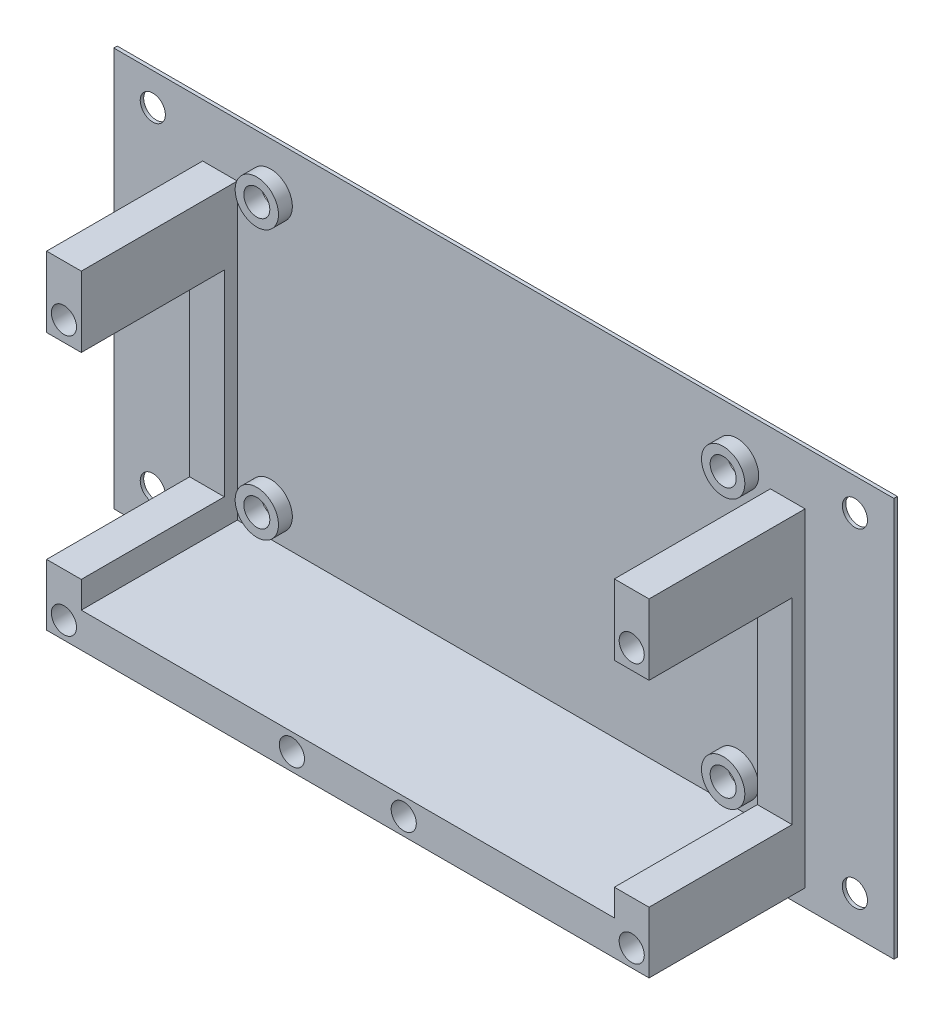
SolidWorks part; units mm, degrees
ref_plane "Ebene vorne" through (0, 0, 0) normal (0, 0, 1) x (1, 0, 0)
ref_plane "Ebene oben" through (0, 0, 0) normal (0, 1, 0) x (1, 0, 0)
ref_plane "Ebene rechts" through (0, 0, 0) normal (1, 0, 0) x (0, 0, -1)
sketch "Skizze1" plane through (0, 0, 0) normal (0, 0, 1) x (1, 0, 0)
  line L1 (-45, -25) -> (45, -25)
  line L2 (-45, -25) -> (-45, 25)
  line L3 (-45, 25) -> (45, 25)
  line L4 (45, -25) -> (45, 25)
  line L5 (-45, -25) -> (45, 25) construction
  line L6 (-45, 25) -> (45, -25) construction
  point P0 (0, 0)
  dimension "D1" = 90
  dimension "D2" = 50
extrude "Aufsatz-Linear austragen1" add sketch "Skizze1" along normal blind 0.4
sketch "Skizze3" plane through (0, 0, 0.4) normal (0, 0, 1) x (1, 0, 0)
  line L1 (-26.9, -11.5381) -> (26.9, -11.5381) construction
  line L2 (-26.9, -11.5381) -> (-26.9, 19.4619) construction
  line L3 (-26.9, 19.4619) -> (26.9, 19.4619) construction
  line L4 (26.9, -11.5381) -> (26.9, 19.4619) construction
  line L5 (-26.9, -11.5381) -> (26.9, 19.4619) construction
  line L6 (-26.9, 19.4619) -> (26.9, -11.5381) construction
  circle A0 centre (-26.9, 19.4619) radius 1.5
  circle A1 centre (26.9, 19.4619) radius 1.5
  circle A2 centre (26.9, -11.5381) radius 1.5
  circle A3 centre (-26.9, -11.5381) radius 1.5
  point P0 (0, 3.9619)
  dimension "D3" = 3
  dimension "D1" = 53.8
  dimension "D2" = 31
extrude "Schnitt-Linear austragen1" cut sketch "Skizze3" against normal through all
sketch "Skizze18" plane through (0, 0, 0.4) normal (0, 0, 1) x (1, 0, 0)
  line L0 (0, 0) -> (0, 9.3339) construction
  line L1 (0, 0) -> (-5.4377, 0) construction
  line L2 (-26.9, 19.4619) -> (-26.9, -11.5381) construction
  line L3 (-26.9, 3.9619) -> (-18.5006, 3.9619) construction
  circle A0 centre (-26.9, 19.4619) radius 2.5
  circle A1 centre (-26.9, 19.4619) radius 1.5
  circle A4 centre (-26.9, 19.4619) radius 1.5 construction
  circle A5 centre (26.9, 19.4619) radius 1.5
  circle A6 centre (26.9, 19.4619) radius 2.5
  circle A7 centre (26.9, -11.5381) radius 2.5
  circle A8 centre (26.9, -11.5381) radius 1.5
  circle A9 centre (-26.9, -11.5381) radius 1.5
  circle A10 centre (-26.9, -11.5381) radius 2.5
  dimension "D1" = 1
extrude "Aufsatz-Linear austragen5" add sketch "Skizze18" along normal blind 1.6
sketch "Skizze4" plane through (0, 0, 0.4) normal (0, 0, 1) x (1, 0, 0)
  line L0 (-26.9, 19.4619) -> (26.9, -11.5381) construction
  line L2 (-30.25, -14.5381) -> (30.25, -14.5381)
  line L3 (-30.25, -14.5381) -> (-30.25, 22.4619)
  line L4 (-30.25, 22.4619) -> (30.25, 22.4619)
  line L5 (30.25, -14.5381) -> (30.25, 22.4619)
  line L6 (-30.25, -14.5381) -> (30.25, 22.4619) construction
  line L7 (-30.25, 22.4619) -> (30.25, -14.5381) construction
  point P4 (0, 3.9619)
  dimension "D1" = 60.5
  dimension "D2" = 37
sketch "Skizze22" plane through (0, 0, 0.4) normal (0, 0, 1) x (1, 0, 0)
  line L0 (30.75, -15.0381) -> (0, -15.0381)
  line L1 (30.75, -15.0381) -> (30.75, -11.9652)
  line L2 (-30.25, -14.5381) -> (30.25, -14.5381) construction
  line L3 (30.25, -14.5381) -> (30.25, 22.4619) construction
  line L5 (0, -19.0381) -> (34.75, -19.0381)
  line L6 (34.75, -19.0381) -> (34.75, -11.9652)
  line L7 (34.75, -11.9652) -> (30.75, -11.9652)
  line L8 (34.75, -19.0381) -> (30.75, -15.0381) construction
  line L9 (32.75, -17.0381) -> (-7.0815, -17.0381) construction
  line L10 (32.75, -17.0381) -> (32.75, 17.6557) construction
  line L11 (34.75, 15.2237) -> (34.75, 18.8333)
  line L13 (34.75, 15.2237) -> (34.75, 10.7001)
  line L14 (34.75, 10.7001) -> (30.75, 10.7001)
  line L15 (30.75, 15.2237) -> (30.75, 10.7001)
  line L16 (34.75, 15.2237) -> (30.75, 10.7001) construction
  line L17 (34.75, 10.7001) -> (30.75, 15.2237) construction
  line L18 (34.75, 18.8333) -> (30.75, 18.8333)
  line L19 (30.75, 18.8333) -> (30.75, 15.2237)
  line L20 (0, 0) -> (0, -7.7771) construction
  line L21 (-34.75, 10.7001) -> (-30.75, 15.2237) construction
  line L22 (-34.75, 15.2237) -> (-30.75, 10.7001) construction
  line L23 (-32.75, -17.0381) -> (-32.75, 17.6557) construction
  line L24 (-34.75, -19.0381) -> (-30.75, -15.0381) construction
  line L25 (-30.75, 18.8333) -> (-30.75, 15.2237)
  line L26 (-34.75, 18.8333) -> (-30.75, 18.8333)
  line L27 (-30.75, 15.2237) -> (-30.75, 10.7001)
  line L28 (-34.75, 10.7001) -> (-30.75, 10.7001)
  line L29 (-34.75, 15.2237) -> (-34.75, 10.7001)
  line L30 (-34.75, 15.2237) -> (-34.75, 18.8333)
  line L31 (-34.75, -11.9652) -> (-30.75, -11.9652)
  line L32 (-34.75, -19.0381) -> (-34.75, -11.9652)
  line L33 (0, -19.0381) -> (-34.75, -19.0381)
  line L35 (-30.75, -15.0381) -> (-30.75, -11.9652)
  line L36 (-30.75, -15.0381) -> (0, -15.0381)
  circle A0 centre (32.75, -17.0381) radius 1.45
  circle A1 centre (6.45, -17.0381) radius 1.45
  circle A2 centre (32.75, 12.9619) radius 1.45
  circle A3 centre (-32.75, 12.9619) radius 1.45
  circle A4 centre (-6.45, -17.0381) radius 1.45
  circle A5 centre (-32.75, -17.0381) radius 1.45
  dimension "D5" = 2.9
  dimension "D1" = 0.5
  dimension "D2" = 0.5
  dimension "D3" = 4
  dimension "D4" = 4
  dimension "D6" = 26.3
  dimension "D7" = 30
extrude "Aufsatz-Linear austragen7" add sketch "Skizze22" along normal blind 18
sketch "Skizze24" plane through (0, 0, 0.4) normal (0, 0, 1) x (1, 0, 0)
  line L0 (-34.75, 10.7001) -> (-34.75, -11.9652)
  line L1 (-34.75, -11.9652) -> (-30.75, -11.9652)
  line L2 (-30.75, -11.9652) -> (-30.75, 10.7001)
  line L3 (-30.75, 10.7001) -> (-34.75, 10.7001)
  line L4 (0, 0) -> (0, 11.0692) construction
  line L5 (30.75, 10.7001) -> (34.75, 10.7001)
  line L6 (30.75, -11.9652) -> (30.75, 10.7001)
  line L7 (34.75, -11.9652) -> (30.75, -11.9652)
  line L8 (34.75, 10.7001) -> (34.75, -11.9652)
extrude "Aufsatz-Linear austragen8" add sketch "Skizze24" along normal blind 1.5
sketch "Skizze23" plane through (0, 0, 0.4) normal (0, 0, 1) x (1, 0, 0)
  line L0 (-43, 23.8) -> (-43, -19.0381)
  line L1 (-43, -19.0381) -> (43, -19.0381)
  line L2 (43, -19.0381) -> (43, 23.8)
  line L3 (43, 23.8) -> (-43, 23.8)
  line L4 (45, 25) -> (-45, 25) construction
  line L5 (-45, 25) -> (-45, -25) construction
  line L7 (45, -25) -> (45, 25) construction
  line L8 (-45, 25) -> (-45, -21.0381)
  line L10 (45, -21.0381) -> (45, 25)
  line L11 (45, 25) -> (-45, 25)
  line L12 (-34.75, -19.0381) -> (34.75, -19.0381) construction
  line L13 (-45, -21.0381) -> (45, -21.0381)
  dimension "D1" = 1.2
  dimension "D2" = 2
  dimension "D3" = 2
  dimension "D4" = 2
extrude "Aufsatz-Linear austragen9" [suppressed] add sketch "Skizze23" along normal blind 50
sketch "Skizze25" plane through (45, 0, 0) normal (1, 0, 0) x (0, 0, -1)
  line L0 (-0.4, -21.0381) -> (-0.4, -25)
  line L1 (-0.4, -25) -> (-0.4, 25) construction
  line L2 (-0.4, -25) -> (0, -25)
  line L3 (0, -25) -> (0, -21.0381)
  line L4 (0, -25) -> (0, 25) construction
  line L5 (0, -21.0381) -> (-0.4, -21.0381)
  line L6 (-18.4, -19.0381) -> (-0.4, -19.0381) construction
  dimension "D1" = 2
extrude "Schnitt-Linear austragen4" cut sketch "Skizze25" against normal through all
sketch "Skizze26" plane through (0, 0, 0) normal (0, 0, -1) x (-1, 0, 0)
  line L0 (0, 0) -> (0, 12.3306)
  line L1 (43, 2.3) -> (22.0124, 2.3) construction
  line L2 (43, 23.8) -> (43, -19.2) construction
  circle A0 centre (40.5, 21.3) radius 1.45
  circle A1 centre (-40.5, 21.3) radius 1.45
  circle A2 centre (-40.5, -16.7) radius 1.45
  circle A3 centre (40.5, -16.7) radius 1.45
extrude "Schnitt-Linear austragen5" cut sketch "Skizze26" against normal blind 1 contours A2 | A1 | A3 | A0
